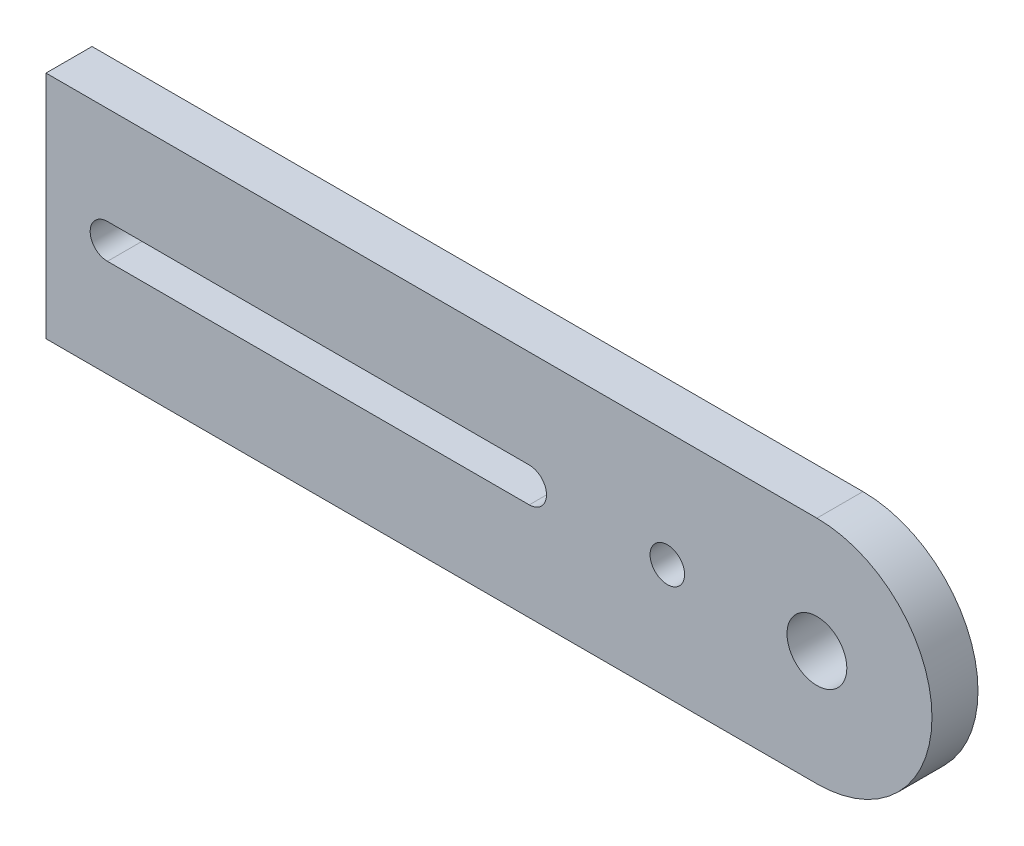
SolidWorks part; units mm, degrees
ref_plane "Front Plane" through (0, 0, 0) normal (0, 0, 1) x (1, 0, 0)
ref_plane "Top Plane" through (0, 0, 0) normal (0, 1, 0) x (1, 0, 0)
ref_plane "Right Plane" through (0, 0, 0) normal (1, 0, 0) x (0, 0, -1)
sketch "Sketch1" plane through (0, 0, 0) normal (0, 0, 1) x (1, 0, 0)
  line L1 (-15, -10) -> (15, -10)
  line L2 (-15, -10) -> (-15, 10)
  line L3 (-15, 10) -> (15, 10)
  line L4 (15, -10) -> (15, 10)
  line L5 (-15, -10) -> (15, 10) construction
  line L6 (-15, 10) -> (15, -10) construction
  circle A0 centre (15, 0) radius 10
  point P0 (0, 0)
  dimension "D1" = 20
  dimension "D2" = 30
extrude "Boss-Extrude1" add sketch "Sketch1" along normal blind 4 contours A0 L3 L2 L1 | L4 A0 | L4 A0
sketch "Sketch2" plane through (0, 0, 4) normal (0, 0, 1) x (1, 0, 0)
  circle A0 centre (15, 0) radius 2.6
  dimension "D1" = 5.2
extrude "Cut-Extrude1" cut sketch "Sketch2" against normal blind 4
sketch "Sketch3" plane through (0, 0, 4) normal (0, 0, 1) x (1, 0, 0)
  line L0 (-15, -10) -> (-15, 10) construction
  line L1 (-15, 10) -> (15, 10) construction
  circle A0 centre (-10, 0) radius 1.5
  circle A1 centre (2, 0) radius 1.5
  dimension "D1" = 3
  dimension "D2" = 5
  dimension "D3" = 3
  dimension "D4" = 10
  dimension "D5" = 12
extrude "Cut-Extrude2" cut sketch "Sketch3" against normal blind 4
fillet "Fillet1" radius 3 2 edges at (-15, -10, 2) (-15, 10, 2)
sketch "Sketch4" plane through (0, 0, 4) normal (0, 0, 1) x (1, 0, 0)
  line L1 (-12, 10) -> (-52, 10)
  line L2 (-12, 10) -> (-12, -10)
  line L3 (-12, -10) -> (-52, -10)
  line L4 (-52, 10) -> (-52, -10)
  dimension "D1" = 40
extrude "Boss-Extrude2" add sketch "Sketch4" against normal blind 4
sketch "Sketch5" plane through (0, 0, 4) normal (0, 0, 1) x (1, 0, 0)
  circle A0 centre (-46.6616, 0) radius 1.5
  dimension "D1" = 3
extrude "Cut-Extrude3" cut sketch "Sketch5" against normal blind 4
sketch "Sketch6" plane through (0, 0, 4) normal (0, 0, 1) x (1, 0, 0)
  line L0 (-46.6616, 1.5) -> (-10, 1.5)
  line L1 (-10, 1.5) -> (-10, -1.5)
  line L2 (-10, -1.5) -> (-46.6616, -1.5)
  line L3 (-46.6616, -1.5) -> (-46.6616, 1.5)
  circle A0 centre (-46.6616, 0) radius 1.5 construction
  circle A1 centre (-10, 0) radius 1.5 construction
extrude "Cut-Extrude4" cut sketch "Sketch6" against normal blind 4
